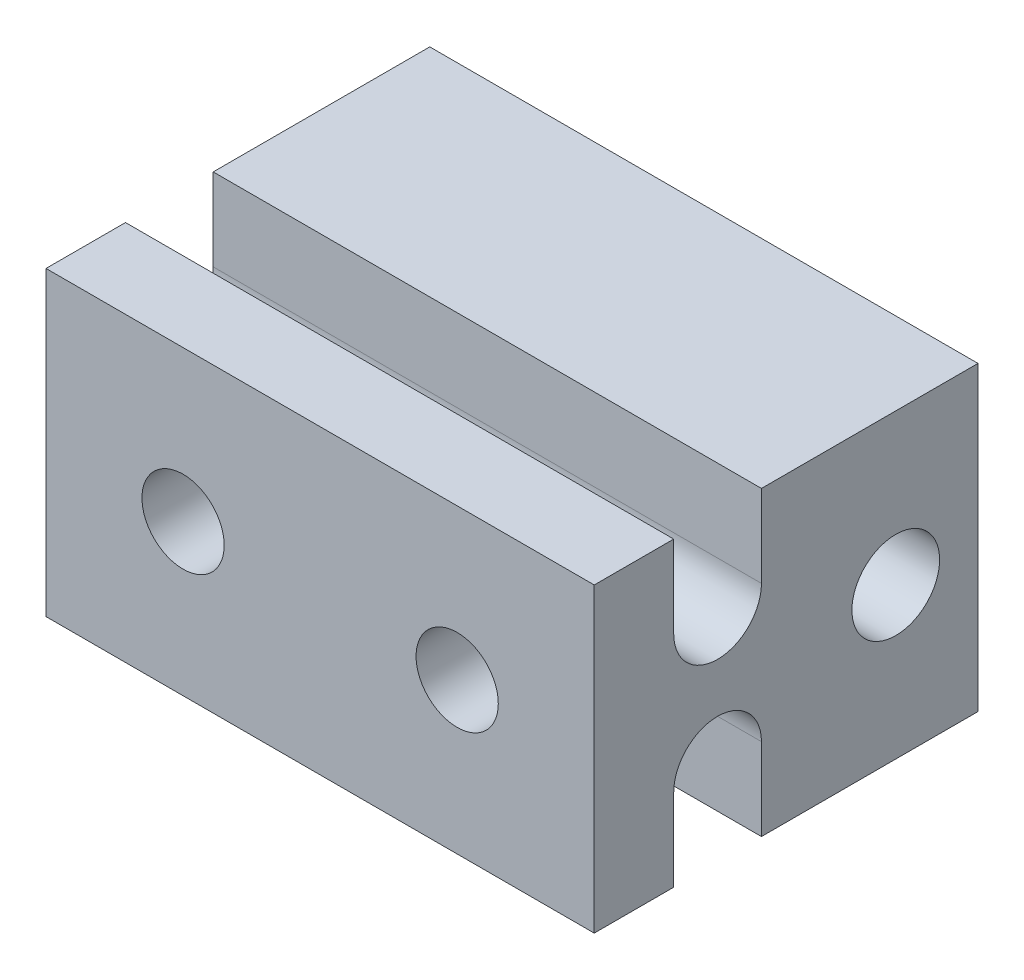
SolidWorks part; units mm, degrees
ref_plane "前视基准面" through (0, 0, 0) normal (0, 0, 1) x (1, 0, 0)
ref_plane "上视基准面" through (0, 0, 0) normal (0, 1, 0) x (1, 0, 0)
ref_plane "右视基准面" through (0, 0, 0) normal (1, 0, 0) x (0, 0, -1)
other "Configuration Table"
sketch "草图2" plane through (0, 0, 0) normal (0, 0, 1) x (1, 0, 0)
  line L1 (-10, 5.5) -> (10, 5.5)
  line L2 (-10, 5.5) -> (-10, -5.5)
  line L3 (-10, -5.5) -> (10, -5.5)
  line L4 (10, 5.5) -> (10, -5.5)
  line L5 (-10, 5.5) -> (10, -5.5) construction
  line L6 (-10, -5.5) -> (10, 5.5) construction
  point P0 (0, 0)
  dimension "D1" = 20
  dimension "D2" = 11
extrude "凸台-拉伸1" add sketch "草图2" against normal blind 14
sketch "草图4" plane through (10, 0, 0) normal (1, 0, 0) x (0, 0, -1)
  line L0 (-0.0574, 0) -> (14, 0) construction
  line L1 (14, -5.5) -> (14, 5.5) construction
  line L2 (0, 2.5) -> (14, 2.5) construction
  line L3 (0, -5.5) -> (0, 5.5) construction
  line L4 (0, -2.5) -> (14, -2.5) construction
  line L5 (4.5, 5.5) -> (4.5, -5.5) construction
  line L6 (14, 5.5) -> (0, 5.5) construction
  line L7 (14, -5.5) -> (0, -5.5) construction
  line L8 (11, 5.5) -> (11, -5.5) construction
  line L9 (2.9, 2.5) -> (2.9, 5.5)
  line L10 (6.1, 2.5) -> (6.1, 5.5327)
  line L11 (2.9, -2.5) -> (2.9, -5.5)
  line L12 (6.1, -2.5) -> (6.1, -5.5)
  arc A0 (2.9, 2.5) -> (6.1, 2.5) centre (4.5, 2.5) ccw
  arc A1 (6.1, -2.5) -> (2.9, -2.5) centre (4.5, -2.5) ccw
  circle A2 centre (11, 0) radius 1.6
  point P18 (4.5, 2.5)
  point P19 (4.5, -2.5)
  point P20 (11, 0)
  line M2 (0, -5.5) -> (14, -5.5)
  line M4 (14, 5.5) -> (0, 5.5)
  dimension "D5" = 3.2
  dimension "D1" = 5
  dimension "D2" = 2.5
  dimension "D3" = 6.5
  dimension "D4" = 3
extrude "切除-拉伸1" cut sketch "草图4" against normal through all contours L12 A1 L11 M2 | L9 A0 L10 M4 | A2
sketch "草图5" plane through (0, 0, 0) normal (0, 0, 1) x (1, 0, 0)
  line L0 (-10.0658, 0) -> (10, 0) construction
  line L1 (10, -5.5) -> (10, 5.5) construction
  line L2 (0, 5.5) -> (0, -5.5) construction
  line L3 (10, 5.5) -> (-10, 5.5) construction
  line L4 (-10, -5.5) -> (10, -5.5) construction
  line L5 (-5, 5.5) -> (-5, -5.5) construction
  line L6 (5, 5.5) -> (5, -5.5) construction
  circle A0 centre (-5, 0) radius 1.5
  circle A1 centre (5, 0) radius 1.5
  point P14 (-5, 0)
  point P15 (5, 0)
  dimension "D3" = 3
  dimension "D1" = 10
  dimension "D2" = 5
extrude "切除-拉伸2" cut sketch "草图5" against normal up to surface (2.9 mm away) up to face at (0, -4, -2.9)
cosmetic thread "装饰螺纹线1" parameters "D2"=4
cosmetic thread "装饰螺纹线2" parameters "D2"=4
